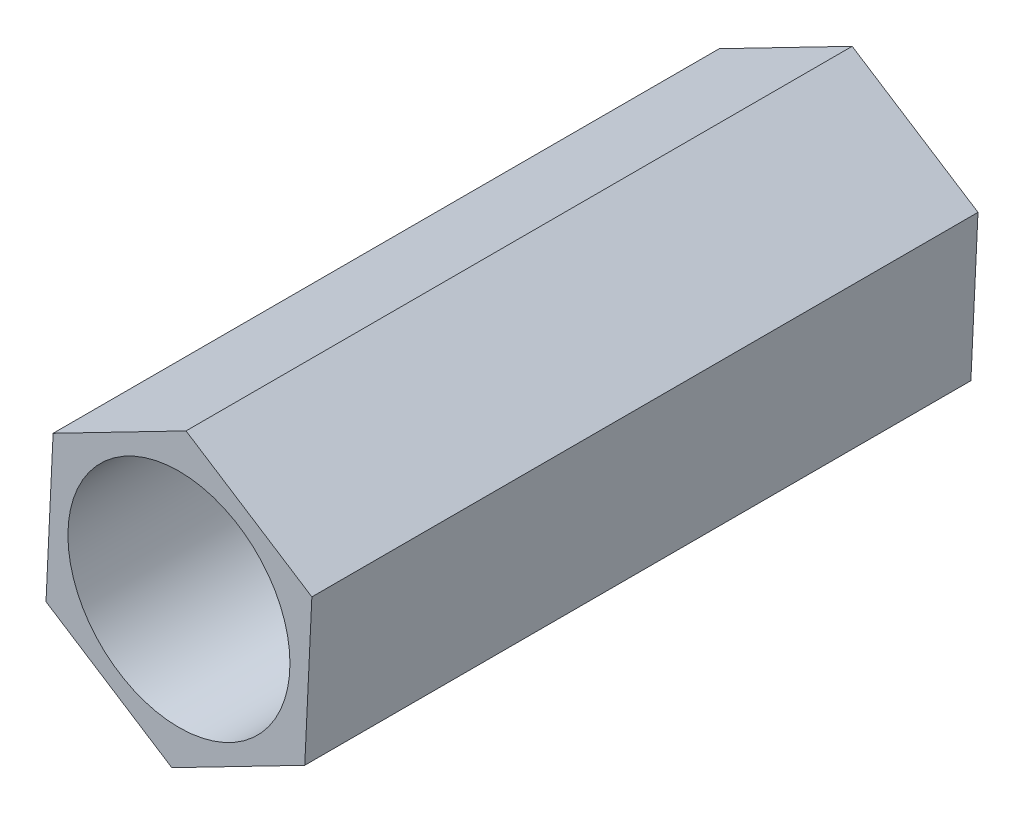
SolidWorks part; units mm, degrees
ref_plane "前视基准面" through (0, 0, 0) normal (0, 0, 1) x (1, 0, 0)
ref_plane "上视基准面" through (0, 0, 0) normal (0, 1, 0) x (1, 0, 0)
ref_plane "右视基准面" through (0, 0, 0) normal (1, 0, 0) x (0, 0, -1)
other "Configuration Table"
sketch "草图1" plane through (0, 0, 0) normal (0, 0, 1) x (1, 0, 0)
  line L1 (-0.096, -2.0184) -> (1.7, -1.0924)
  line L2 (1.7, -1.0924) -> (1.796, 0.926)
  line L3 (1.796, 0.926) -> (0.096, 2.0184)
  line L4 (0.096, 2.0184) -> (-1.7, 1.0924)
  line L5 (-1.7, 1.0924) -> (-1.796, -0.926)
  line L6 (-1.796, -0.926) -> (-0.096, -2.0184)
  circle A0 centre (0, 0) radius 1.75 construction
  dimension "D1" = 3.5
  dimension "D2" = 1.7
extrude "凸台-拉伸1" add sketch "草图1" against normal blind 9
sketch "草图2" plane through (0, 0, 0) normal (0, 0, 1) x (1, 0, 0)
  circle A0 centre (0, 0) radius 1.5
  dimension "D1" = 3
extrude "切除-拉伸1" cut sketch "草图2" against normal through all
cosmetic thread "装饰螺纹线1"
